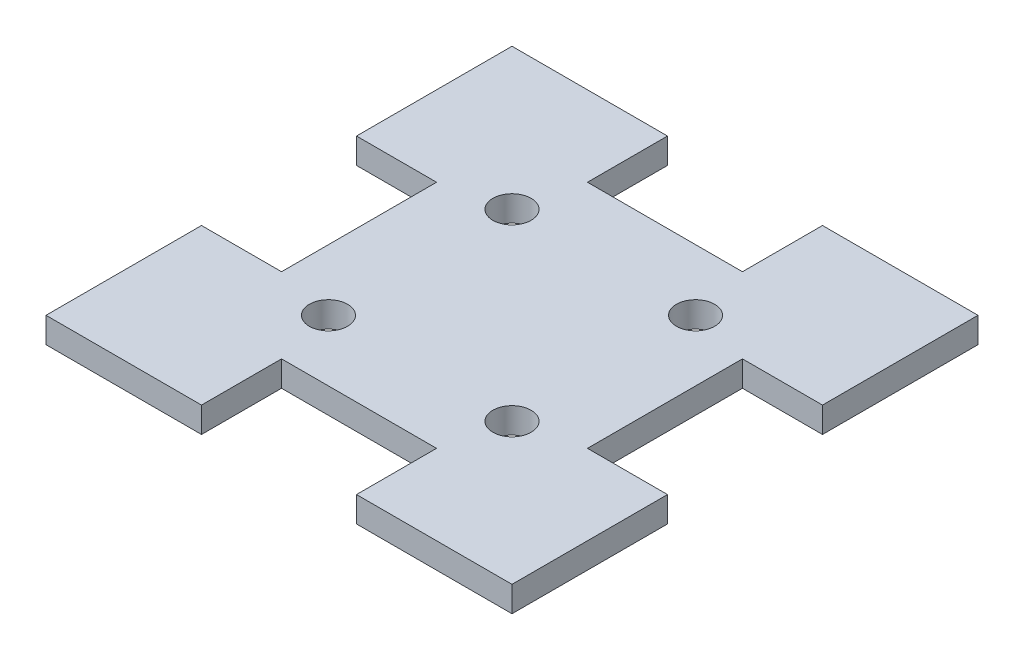
SolidWorks part; units mm, degrees
material "ASTM A36 Steel"
ref_plane "Front Plane" through (0, 0, 0) normal (0, 0, 1) x (1, 0, 0)
ref_plane "Top Plane" through (0, 0, 0) normal (0, 1, 0) x (1, 0, 0)
ref_plane "Right Plane" through (0, 0, 0) normal (1, 0, 0) x (0, 0, -1)
sketch "Sketch1" plane through (0, 0, 0) normal (0, 1, 0) x (1, 0, 0)
  line L0 (0, -49.6144) -> (0, 49.6144) construction
  line L1 (-58.039, -58.039) -> (58.039, -58.039)
  line L2 (-58.039, -58.039) -> (-58.039, 58.039)
  line L3 (-58.039, 58.039) -> (58.039, 58.039)
  line L4 (58.039, -58.039) -> (58.039, 58.039)
  line L5 (-58.039, -58.039) -> (58.039, 58.039) construction
  line L6 (-58.039, 58.039) -> (58.039, -58.039) construction
  line L7 (-19.304, -38.1) -> (19.304, -38.1)
  line L8 (-19.304, -38.1) -> (-19.304, -58.039)
  line L9 (-19.304, -58.039) -> (19.304, -58.039)
  line L10 (19.304, -38.1) -> (19.304, -58.039)
  line L11 (-19.304, -38.1) -> (19.304, -58.039) construction
  line L12 (-19.304, -58.039) -> (19.304, -38.1) construction
  line L13 (-72.7085, 0) -> (72.7085, 0) construction
  line L14 (19.304, 38.1) -> (-19.304, 38.1)
  line L15 (19.304, 38.1) -> (19.304, 58.039)
  line L16 (19.304, 58.039) -> (-19.304, 58.039)
  line L17 (-19.304, 38.1) -> (-19.304, 58.039)
  line L18 (19.304, 38.1) -> (-19.304, 58.039) construction
  line L19 (19.304, 58.039) -> (-19.304, 38.1) construction
  line L20 (-38.1, 19.304) -> (-58.039, 19.304)
  line L21 (-38.1, 19.304) -> (-38.1, -19.304)
  line L22 (-38.1, -19.304) -> (-58.039, -19.304)
  line L23 (-58.039, 19.304) -> (-58.039, -19.304)
  line L24 (-38.1, 19.304) -> (-58.039, -19.304) construction
  line L25 (-38.1, -19.304) -> (-58.039, 19.304) construction
  line L27 (38.1, 19.304) -> (58.039, 19.304)
  line L28 (38.1, 19.304) -> (38.1, -19.304)
  line L29 (38.1, -19.304) -> (58.039, -19.304)
  line L30 (58.039, 19.304) -> (58.039, -19.304)
  line L31 (38.1, 19.304) -> (58.039, -19.304) construction
  line L32 (38.1, -19.304) -> (58.039, 19.304) construction
  line L33 (-19.05, -38.1) -> (19.05, -38.1) construction
  line L34 (-19.05, -38.1) -> (-19.05, -76.2) construction
  line L35 (-19.05, -76.2) -> (19.05, -76.2) construction
  line L36 (19.05, -38.1) -> (19.05, -76.2) construction
  line L37 (-19.05, -38.1) -> (19.05, -76.2) construction
  line L38 (-19.05, -76.2) -> (19.05, -38.1) construction
  point P0 (0, 0)
  point P6 (0, -48.0695)
  point P13 (0, 48.0695)
  point P18 (-48.0695, 0)
  point P25 (48.0695, 0)
  point P30 (0, -57.15)
  dimension "D1" = 116.078
  dimension "D2" = 116.078
  dimension "D3" = 76.2
  dimension "D4" = 38.1
  dimension "D5" = 38.1
  dimension "D6" = 0.254
extrude "Boss-Extrude1" add sketch "Sketch1" along normal mid plane 6.35 contours L29 L28 L27 L4 L3 L15 L14 L17 L2 L20 L21 L22 L1 L8 L7 L10
sketch "Sketch2" plane through (0, 3.175, 0) normal (0, 1, 0) x (1, 0, 0)
  line L1 (22.86, 22.86) -> (-22.86, 22.86) construction
  line L2 (22.86, 22.86) -> (22.86, -22.86) construction
  line L3 (22.86, -22.86) -> (-22.86, -22.86) construction
  line L4 (-22.86, 22.86) -> (-22.86, -22.86) construction
  line L5 (22.86, 22.86) -> (-22.86, -22.86) construction
  line L6 (22.86, -22.86) -> (-22.86, 22.86) construction
  circle A0 centre (-22.86, 22.86) radius 4.7625
  circle A1 centre (-22.86, -22.86) radius 4.7625
  circle A2 centre (22.86, -22.86) radius 4.7625
  circle A3 centre (22.86, 22.86) radius 4.7625
  point P0 (0, 0)
  dimension "D3" = 9.525
  dimension "D1" = 45.72
  dimension "D2" = 45.72
extrude "Cut-Extrude1" cut sketch "Sketch2" against normal through all
sketch3d "TAG"
  line L0 (-58.039, 3.175, -58.039) -> (-58.039, 3.175, 58.039)
  line L1 (-58.039, 3.175, -19.304) -> (-58.039, 3.175, -58.039) construction
  line L2 (-58.039, 3.175, 58.039) -> (58.039, 3.175, 58.039)
  line L3 (-58.039, 3.175, 58.039) -> (-58.039, -3.175, 58.039)
  line L4 (-58.039, 3.175, 58.039) -> (-58.039, -3.175, 58.039) construction
  line L5 (-58.039, -3.175, 58.039) -> (-58.039, -3.175, 19.304) construction
  dimension "D1" = 6.35
  dimension "D2" = 116.078
  dimension "D3" = 116.078
